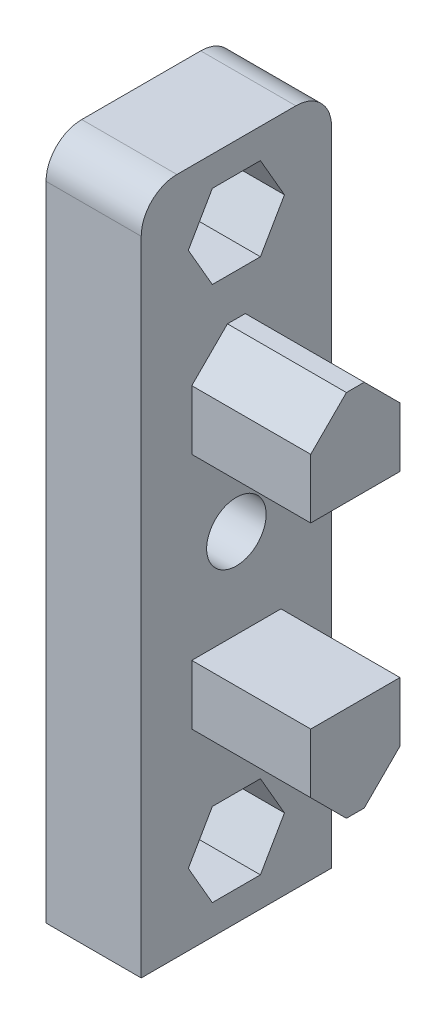
SolidWorks part; units mm, degrees
ref_plane "Plan de face" through (0, 0, 0) normal (0, 0, 1) x (1, 0, 0)
ref_plane "Plan de dessus" through (0, 0, 0) normal (0, 1, 0) x (1, 0, 0)
ref_plane "Plan de droite" through (0, 0, 0) normal (1, 0, 0) x (0, 0, -1)
sketch "Esquisse1" plane through (0, 0, 0) normal (1, 0, 0) x (0, 0, -1)
  line L1 (-8, 14.25) -> (8, 14.25)
  line L2 (-8, 14.25) -> (-8, -14.25)
  line L3 (-8, -14.25) -> (8, -14.25)
  line L4 (8, 14.25) -> (8, -14.25)
  line L5 (-8, 14.25) -> (8, -14.25) construction
  line L6 (-8, -14.25) -> (8, 14.25) construction
  point P0 (0, 0)
  dimension "D1" = 16
  dimension "D2" = 28.5
extrude "Boss.-Extru.1" add sketch "Esquisse1" along normal blind 8
sketch "Esquisse2" plane through (8, 0, 0) normal (1, 0, 0) x (0, 0, -1)
  line L0 (0, 0) -> (0, 8.25) construction
  line L1 (4.0415, 8.25) -> (2.0207, 11.75)
  line L2 (2.0207, 11.75) -> (-2.0207, 11.75)
  line L3 (-2.0207, 11.75) -> (-4.0415, 8.25)
  line L4 (-4.0415, 8.25) -> (-2.0207, 4.75)
  line L5 (-2.0207, 4.75) -> (2.0207, 4.75)
  line L6 (2.0207, 4.75) -> (4.0415, 8.25)
  line L7 (8, 14.25) -> (-8, 14.25) construction
  circle A0 centre (0, 8.25) radius 3.5 construction
  dimension "D1" = 7
  dimension "D2" = 6
extrude "Enlèv. mat.-Extru.1" cut sketch "Esquisse2" against normal blind 5.5
sketch "Esquisse3" plane through (2.5, 0, 0) normal (1, 0, 0) x (0, 0, -1)
  line L0 (0, 0) -> (0, 8.25) construction
  line L1 (0, 8.25) -> (4.0415, 8.25) construction
  circle A0 centre (0, 8.25) radius 2.5
  dimension "D1" = 5
extrude "Enlèv. mat.-Extru.2" cut sketch "Esquisse3" against normal through all
sketch "Esquisse4" plane through (8, 0, 0) normal (1, 0, 0) x (0, 0, -1)
  line L0 (0, 0) -> (0, -2.75) construction
  line L1 (-3.75, 1.25) -> (3.75, 1.25)
  line L2 (-3.75, 1.25) -> (-3.75, -6.75)
  line L3 (-3.75, -6.75) -> (3.75, -6.75)
  line L4 (3.75, 1.25) -> (3.75, -6.75)
  line L5 (-3.75, 1.25) -> (3.75, -6.75) construction
  line L6 (-3.75, -6.75) -> (3.75, 1.25) construction
  line L7 (8, 14.25) -> (-8, 14.25) construction
  point P0 (0, -2.75)
  dimension "D1" = 8
  dimension "D2" = 21
  dimension "D3" = 7.5
extrude "Boss.-Extru.2" add sketch "Esquisse4" along normal blind 10
chamfer "Chanfrein2" distance 3 angle 45 2 edges at (13, 1.25, -3.75) (13, 1.25, 3.75)
mirror "Symétrie1" about plane through (8, -14.25, 8) normal (0, 1, 0) of bodies 104
sketch "Esquisse5" plane through (8, 0, 0) normal (1, 0, 0) x (0, 0, -1)
  line L0 (0, 0) -> (0, -14.25) construction
  line L1 (-8, -14.25) -> (0, -14.25) construction
  line L2 (-8, 14.25) -> (-8, -42.75) construction
  circle A0 centre (0, -14.25) radius 2.5
  dimension "D1" = 5
extrude "Enlèv. mat.-Extru.3" cut sketch "Esquisse5" against normal through all
fillet "Congé1" radius 3 2 edges at (4, 14.25, -8) (4, 14.25, 8)
